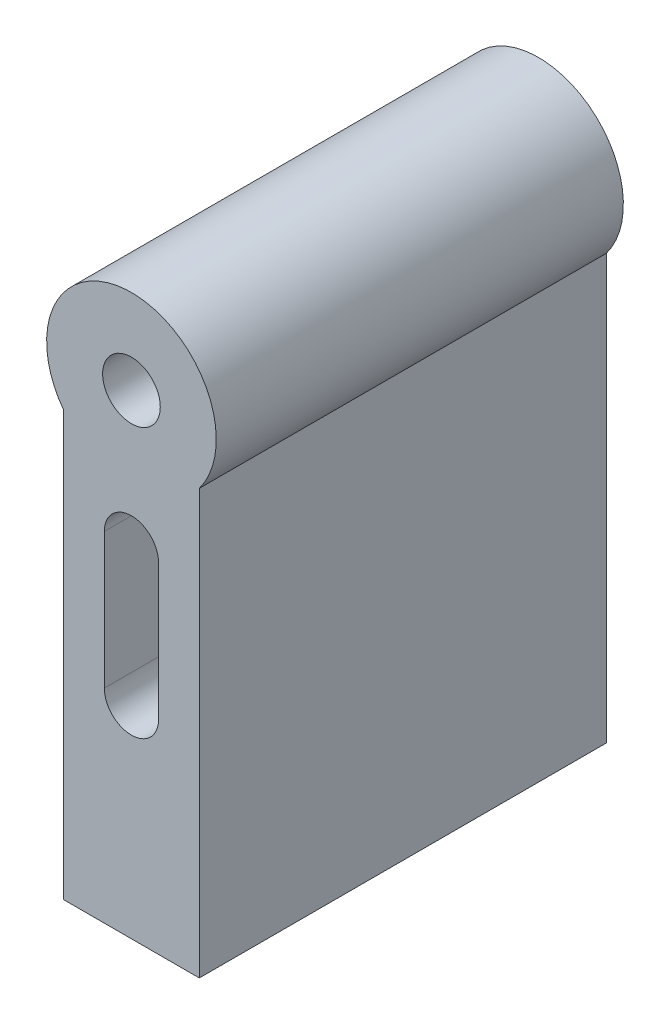
SolidWorks part; units mm, degrees
material "ABS"
ref_plane "Front" through (0, 0, 0) normal (0, 0, 1) x (1, 0, 0)
ref_plane "Top" through (0, 0, 0) normal (0, 1, 0) x (1, 0, 0)
ref_plane "Right" through (0, 0, 0) normal (1, 0, 0) x (0, 0, -1)
sketch "Croquis1" plane through (0, 0, 0) normal (0, 0, 1) x (1, 0, 0)
  line L0 (-4, -3) -> (-4, -28)
  line L1 (-4, -28) -> (4, -28)
  line L4 (4, -28) -> (4, -3)
  line L5 (0, -8) -> (0, -16) construction
  line L6 (1.6, -8) -> (1.6, -16)
  line L7 (-1.6, -8) -> (-1.6, -16)
  circle A0 centre (0, 0) radius 1.7
  arc A1 (-4, -3) -> (4, -3) centre (0, 0) cw
  arc A2 (1.6, -8) -> (-1.6, -8) centre (0, -8) ccw
  arc A3 (-1.6, -16) -> (1.6, -16) centre (0, -16) ccw
  point P9 (0, -12)
  dimension "D1" = 3.4
  dimension "D2" = 5
  dimension "D4" = 28
  dimension "D3" = 8
  dimension "D5" = 2.4
  dimension "D6" = 8
  dimension "D7" = 8
extrude "Saliente-Extruir1" add sketch "Croquis1" along normal mid plane 24
ref_plane "Plano1" through (0, -24.2, 0) normal (0, -1, 0) x (-1, 0, 0)
sketch "Croquis2" plane through (0, -28, 0) normal (0, -1, 0) x (1, 0, 0)
  circle A0 centre (0, -7) radius 1.7
  dimension "D1" = 3.4
  dimension "D2" = 7
extrude "TORNILLO" cut sketch "Croquis2" against normal blind 10
sketch "Croquis3" plane through (0, -24.2, 0) normal (0, -1, 0) x (-1, 0, 0)
  line L0 (1.7032, 9.95) -> (5, 9.95)
  line L1 (-1.7032, 9.95) -> (-3.4064, 7)
  line L2 (-3.4064, 7) -> (-1.7032, 4.05)
  line L3 (-1.7032, 4.05) -> (1.7032, 4.05)
  line L4 (1.7032, 4.05) -> (3.4064, 7) construction
  line L5 (3.4064, 7) -> (1.7032, 9.95) construction
  line L6 (1.7032, 9.95) -> (-1.7032, 9.95)
  line L8 (5, 9.95) -> (5, 4.05)
  line L10 (5, 4.05) -> (1.7032, 4.05)
  line L11 (5, -12) -> (5, 12) construction
  circle A0 centre (0, 7) radius 2.95 construction
  dimension "D1" = 5.9
extrude "TUERCA" cut sketch "Croquis3" against normal blind 4
mirror "Simetría1" about plane through (0, 0, 0) normal (0, 0, 1) of "TUERCA", "TORNILLO"
